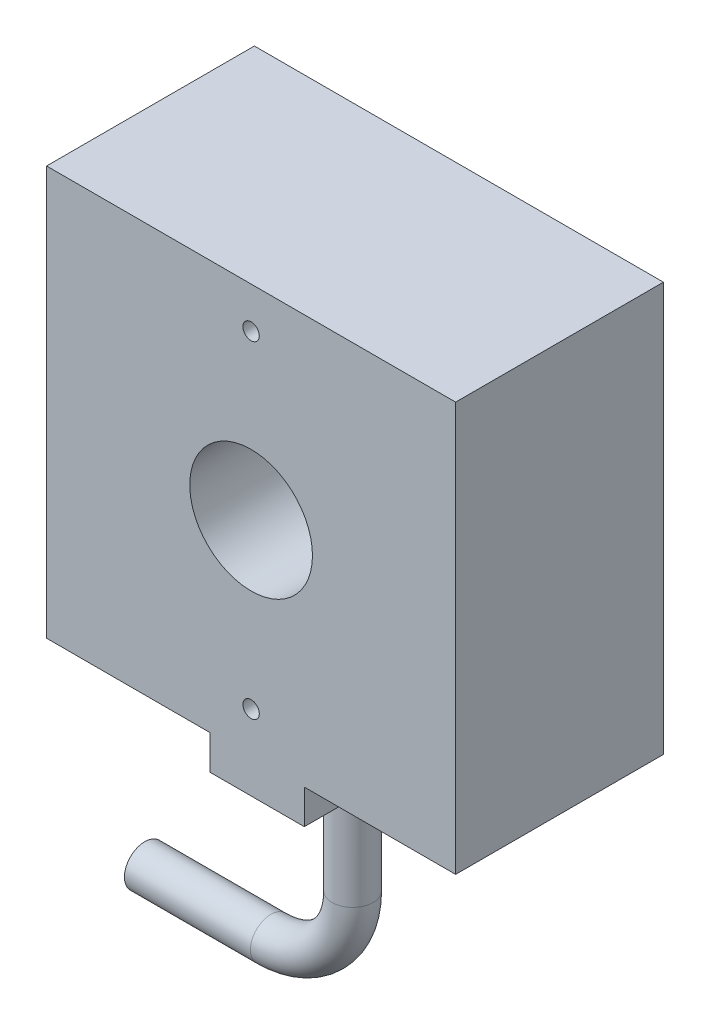
SolidWorks part; units mm, degrees
ref_plane "Front Plane" through (0, 0, 0) normal (0, 0, 1) x (1, 0, 0)
ref_plane "Top Plane" through (0, 0, 0) normal (0, 1, 0) x (1, 0, 0)
ref_plane "Right Plane" through (0, 0, 0) normal (1, 0, 0) x (0, 0, -1)
sketch "Sketch1" plane through (0, 0, 0) normal (0, 0, 1) x (1, 0, 0)
  line L1 (0, 0) -> (50, 0)
  line L2 (0, 0) -> (0, 50)
  line L3 (0, 50) -> (50, 50)
  line L4 (50, 0) -> (50, 50)
  dimension "D1" = 50
  dimension "D2" = 50
extrude "Boss-Extrude1" add sketch "Sketch1" along normal blind 25.4
sketch "Sketch2" plane through (0, 0, 25.4) normal (0, 0, 1) x (1, 0, 0)
  line L0 (0, 0) -> (50, 0) construction
  line L1 (50, 0) -> (50, 50) construction
  circle A0 centre (25, 25) radius 7.5
  circle A1 centre (25, 45) radius 1
  circle A2 centre (25, 5) radius 1
  dimension "D1" = 15
  dimension "D2" = 2
  dimension "D3" = 2
  dimension "D4" = 20
  dimension "D5" = 20
  dimension "D7" = 25
  dimension "D8" = 25
  dimension "D9" = 25
  dimension "D6" = 25
extrude "Cut-Extrude1" cut sketch "Sketch2" against normal through all
sketch "Sketch3" plane through (0, 0, 25.4) normal (0, 0, 1) x (1, 0, 0)
  line L0 (0, 0) -> (50, 0) construction
  line L1 (19.9993, 0) -> (31.5063, 0)
  line L2 (19.9993, 0) -> (19.9993, -4.1975)
  line L3 (19.9993, -4.1975) -> (31.5063, -4.1975)
  line L4 (31.5063, 0) -> (31.5063, -4.1975)
extrude "Boss-Extrude2" add sketch "Sketch3" against normal up to surface (25.4 mm away) up to face at (26, 5, 0)
sketch "Sketch4" plane through (0, -4.1975, 0) normal (0, -1, 0) x (1, 0, 0)
  circle A0 centre (25.8368, 13.8253) radius 2.5
  dimension "D1" = 5
ref_plane "Plane1" through (0, 0, 13.8253) normal (0, 0, -1) x (-1, 0, 0)
sketch "Sketch5" plane through (0, 0, 13.8253) normal (0, 0, -1) x (-1, 0, 0)
  line L0 (-25.8368, -4.1975) -> (-25.8368, -19.5975)
  line L1 (-28.3368, -4.1975) -> (-23.3368, -4.1975) construction
  line L2 (-15.8368, -29.5975) -> (-0.4368, -29.5975)
  arc A0 (-25.8368, -19.5975) -> (-15.8368, -29.5975) centre (-15.8368, -19.5975) ccw
  dimension "D1" = 10
sweep "Sweep1" add profiles "Sketch4" path "Sketch5"
